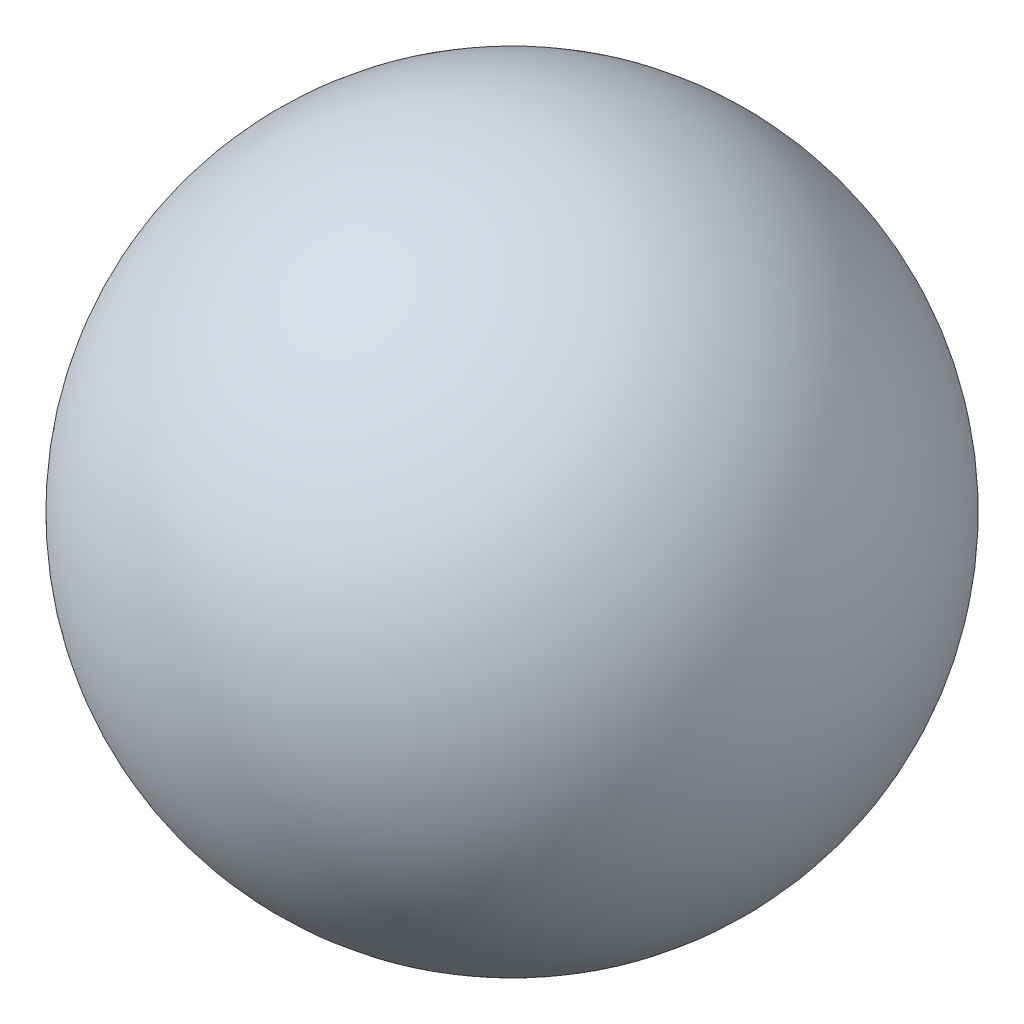
SolidWorks part; units mm, degrees
ref_plane "前视基准面" through (0, 0, 0) normal (0, 0, 1) x (1, 0, 0)
ref_plane "上视基准面" through (0, 0, 0) normal (0, 1, 0) x (1, 0, 0)
ref_plane "右视基准面" through (0, 0, 0) normal (1, 0, 0) x (0, 0, -1)
sketch "草图1" plane through (0, 0, 0) normal (0, 0, 1) x (1, 0, 0)
  line L0 (-1.7606, 21) -> (-1.7606, -21)
  arc A0 (-1.7606, -21) -> (-1.7606, 21) centre (-1.7606, 0) ccw
revolve "旋转1" add sketch "草图1" angle 360 about L0
